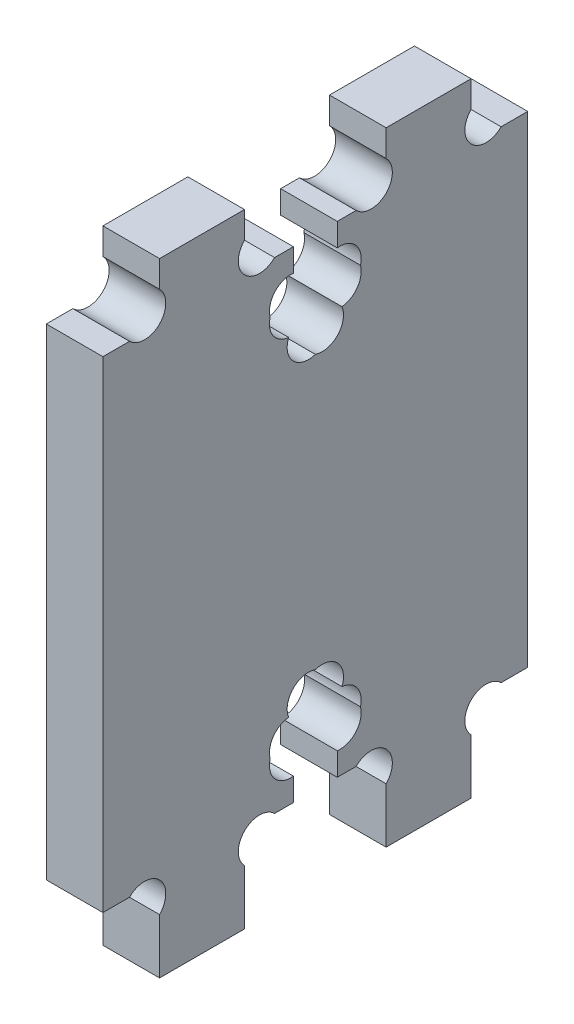
SolidWorks part; units mm, degrees
ref_plane "Alzado" through (0, 0, 0) normal (0, 0, 1) x (1, 0, 0)
ref_plane "Planta" through (0, 0, 0) normal (0, 1, 0) x (1, 0, 0)
ref_plane "Vista lateral" through (0, 0, 0) normal (1, 0, 0) x (0, 0, -1)
sketch "Croquis1" plane through (0, 0, 0) normal (1, 0, 0) x (0, -1, 0)
  line L1 (-17, -15) -> (17, -15)
  line L2 (-17, -15) -> (-17, 15)
  line L3 (-17, 15) -> (17, 15)
  line L4 (17, -15) -> (17, 15)
  line L5 (-17, -15) -> (17, 15) construction
  line L6 (-17, 15) -> (17, -15) construction
  point P0 (0, 0)
  dimension "D1" = 30
  dimension "D2" = 34
extrude "Saliente-Extruir1" add sketch "Croquis1" along normal blind 4
sketch "Croquis2" plane through (4, 0, 0) normal (1, 0, 0) x (0, 0, -1)
  line L0 (-15, -17) -> (15, -17) construction
  line L1 (-11, -17) -> (-5, -17)
  line L2 (-11, -17) -> (-11, -21)
  line L3 (-11, -21) -> (-5, -21)
  line L4 (-5, -17) -> (-5, -21)
  line L5 (-11, -17) -> (-15, -17) construction
  line L6 (5, -17) -> (11, -17)
  line L7 (5, -17) -> (5, -21)
  line L8 (5, -21) -> (11, -21)
  line L9 (11, -17) -> (11, -21)
  line L10 (0, 0) -> (11.6283, 0) construction
  line L11 (11, 17) -> (11, 21)
  line L12 (15, -17) -> (11, -17) construction
  line L13 (5, 21) -> (11, 21)
  line L14 (5, 17) -> (5, 21)
  line L15 (5, 17) -> (11, 17)
  line L16 (-5, 17) -> (-5, 21)
  line L17 (-11, 21) -> (-5, 21)
  line L18 (-11, 17) -> (-11, 21)
  line L19 (-11, 17) -> (-5, 17)
  dimension "D1" = 4
  dimension "D2" = 6
  dimension "D3" = 4
extrude "Saliente-Extruir2" add sketch "Croquis2" against normal through all
sketch "Croquis3" plane through (4, 0, 0) normal (1, 0, 0) x (0, 0, -1)
  line L0 (-1.55, 17) -> (-1.55, 14.95)
  line L1 (5, 17) -> (-5, 17) construction
  line L2 (-1.55, 14.95) -> (-2.8, 14.95)
  line L3 (-2.8, 14.95) -> (-2.8, 12.05)
  line L4 (-2.8, 12.05) -> (-1.55, 12.05)
  line L5 (2.8, 12.05) -> (2.8, 14.95)
  line L6 (2.8, 14.95) -> (1.55, 14.95)
  line L7 (1.55, 14.95) -> (1.55, 17)
  line L8 (1.55, 17) -> (-1.55, 17)
  line L9 (-5, 21) -> (5, 21) construction
  line L10 (0, 10) -> (0, 17) construction
  line L11 (0, 17) -> (0, 21) construction
  line L12 (-1.55, 12.05) -> (-1.55, 10)
  line L13 (-1.55, 10) -> (1.55, 10)
  line L14 (1.55, 10) -> (1.55, 12.05)
  line L15 (1.55, 12.05) -> (2.8, 12.05)
  line L16 (0, 13.5) -> (-2.8, 13.5) construction
  line L17 (0, 0) -> (12.012, 0) construction
  line L18 (1.55, -12.05) -> (2.8, -12.05)
  line L19 (1.55, -10) -> (1.55, -12.05)
  line L20 (-1.55, -10) -> (1.55, -10)
  line L21 (-1.55, -12.05) -> (-1.55, -10)
  line L22 (1.55, -17) -> (-1.55, -17)
  line L23 (1.55, -14.95) -> (1.55, -17)
  line L24 (2.8, -14.95) -> (1.55, -14.95)
  line L25 (2.8, -12.05) -> (2.8, -14.95)
  line L26 (-2.8, -12.05) -> (-1.55, -12.05)
  line L27 (-2.8, -14.95) -> (-2.8, -12.05)
  line L28 (-1.55, -14.95) -> (-2.8, -14.95)
  line L29 (-1.55, -17) -> (-1.55, -14.95)
  dimension "D1" = 3.1
  dimension "D2" = 5.6
  dimension "D3" = 7
  dimension "D4" = 2.9
extrude "Cortar-Extruir1" cut sketch "Croquis3" against normal through all
sketch "Croquis4" plane through (4, 0, 0) normal (1, 0, 0) x (0, 0, -1)
  line L1 (-11, -21) -> (-5, -21)
  line L2 (-11, -21) -> (-11, -23)
  line L3 (-11, -23) -> (-5, -23)
  line L4 (-5, -21) -> (-5, -23)
  line L5 (5, -21) -> (11, -21)
  line L6 (5, -21) -> (5, -23)
  line L7 (5, -23) -> (11, -23)
  line L8 (11, -21) -> (11, -23)
  dimension "D1" = 2
extrude "Saliente-Extruir3" add sketch "Croquis4" against normal through all
sketch "Croquis5" plane through (4, 0, 0) normal (1, 0, 0) x (0, 0, -1)
  line L0 (-11, -17) -> (-12.5, -18.5) construction
  line L1 (-15, -17) -> (-11, -17) construction
  line L2 (-11, -17) -> (-11, -23) construction
  line L3 (-8, -23) -> (-8, -14.3264) construction
  line L4 (-11, -23) -> (-5, -23) construction
  line L5 (0, 0) -> (0, -7.0467) construction
  line L6 (0, 0) -> (10.2719, 0) construction
  circle A0 centre (-12.5, -18.5) radius 1.5 construction
  circle A1 centre (-12.0607, -18.0607) radius 1.5
  circle A2 centre (-3.9393, -18.0607) radius 1.5
  circle A3 centre (12.0607, -18.0607) radius 1.5
  circle A4 centre (3.9393, -18.0607) radius 1.5
  circle A5 centre (-12.0607, 18.0607) radius 1.5
  circle A6 centre (-3.9393, 18.0607) radius 1.5
  circle A7 centre (3.9393, 18.0607) radius 1.5
  circle A8 centre (12.0607, 18.0607) radius 1.5
  dimension "D1" = 3
extrude "Cortar-Extruir2" cut sketch "Croquis5" against normal through all
sketch "Croquis6" plane through (4, 0, 0) normal (1, 0, 0) x (0, 0, -1)
  line L1 (-1.55, -10) -> (-0.05, -11.5) construction
  line L2 (-1.55, -10) -> (-1.55, -12.05) construction
  line L3 (1.55, -10) -> (-1.55, -10) construction
  line L4 (0, 0) -> (0, -6.7537) construction
  line L5 (0, 0) -> (10.574, 0) construction
  circle A0 centre (-0.05, -11.5) radius 1.5 construction
  arc A1 (0, -9.6427) -> (0, -12.4786) centre (-0.4893, -11.0607) ccw
  arc A2 (0, -9.6427) -> (0, -12.4786) centre (0.4893, -11.0607) cw
  arc A3 (0, 9.6427) -> (0, 12.4786) centre (-0.4893, 11.0607) cw
  arc A4 (0, 9.6427) -> (0, 12.4786) centre (0.4893, 11.0607) ccw
  dimension "D1" = 3
extrude "Cortar-Extruir4" cut sketch "Croquis6" against normal through all
sketch "Croquis7" plane through (4, 0, 0) normal (1, 0, 0) x (0, 0, -1)
  line L0 (-1.6168, -12.05) -> (-2.8, -12.05) construction
  line L1 (-2.8, -12.05) -> (-2.8, -14.95) construction
  line L2 (-2.8, -12.05) -> (-1.3, -13.55) construction
  line L3 (0, 0) -> (0, -6.2751) construction
  line L5 (2.8, -13.5) -> (1.3633, -13.5) construction
  line L6 (2.8, -14.95) -> (2.8, -12.05) construction
  line L7 (0, 0) -> (6.2309, 0) construction
  circle A0 centre (-1.3, -13.55) radius 1.5 construction
  arc A1 (-0.2907, -13.5) -> (-3.1879, -13.5) centre (-1.7393, -13.1107) ccw
  arc A2 (0.2907, -13.5) -> (3.1879, -13.5) centre (1.7393, -13.1107) cw
  arc A3 (-0.2907, -13.5) -> (-3.1879, -13.5) centre (-1.7393, -13.8893) cw
  arc A4 (0.2907, -13.5) -> (3.1879, -13.5) centre (1.7393, -13.8893) ccw
  arc A6 (0.2907, 13.5) -> (3.1879, 13.5) centre (1.7393, 13.1107) ccw
  arc A7 (0.2907, 13.5) -> (3.1879, 13.5) centre (1.7393, 13.8893) cw
  arc A8 (-0.2907, 13.5) -> (-3.1879, 13.5) centre (-1.7393, 13.8893) ccw
  arc A9 (-0.2907, 13.5) -> (-3.1879, 13.5) centre (-1.7393, 13.1107) cw
  dimension "D1" = 3
extrude "Cortar-Extruir6" cut sketch "Croquis7" against normal through all
